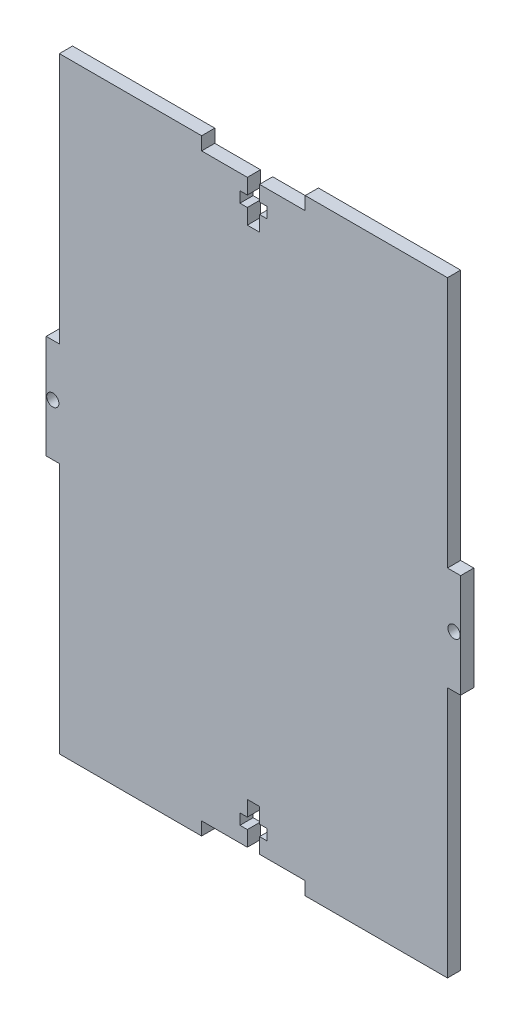
SolidWorks part; units mm, degrees
ref_plane "Front Plane" through (0, 0, 0) normal (0, 0, 1) x (1, 0, 0)
ref_plane "Top Plane" through (0, 0, 0) normal (0, 1, 0) x (1, 0, 0)
ref_plane "Right Plane" through (0, 0, 0) normal (1, 0, 0) x (0, 0, -1)
sketch "Sketch1" plane through (0, 0, 0) normal (0, 0, 1) x (1, 0, 0)
  line L0 (0, 73.175) -> (0, -73.175) construction
  line L1 (-46.825, 73.175) -> (46.825, 73.175)
  line L2 (-46.825, 73.175) -> (-46.825, -73.175)
  line L3 (-46.825, -73.175) -> (46.825, -73.175)
  line L4 (46.825, 73.175) -> (46.825, -73.175)
  line L5 (-46.825, 73.175) -> (46.825, -73.175) construction
  line L6 (-46.825, -73.175) -> (46.825, 73.175) construction
  line L7 (-46.825, 0) -> (46.825, 0) construction
  line L8 (-3.25, -63.7) -> (3.25, -63.7)
  line L9 (12.5, 73.175) -> (-12.5, 73.175)
  line L10 (12.5, 73.175) -> (12.5, 70)
  line L11 (12.5, 70) -> (-12.5, 70)
  line L12 (-12.5, 73.175) -> (-12.5, 70)
  line L13 (12.5, 73.175) -> (-12.5, 70) construction
  line L14 (12.5, 70) -> (-12.5, 73.175) construction
  line L15 (-1.47, 70) -> (1.47, 70)
  line L16 (-1.47, 70) -> (-1.47, 60)
  line L17 (-1.47, 60) -> (1.47, 60)
  line L18 (1.47, 70) -> (1.47, 60)
  line L19 (-1.47, 70) -> (1.47, 60) construction
  line L20 (-1.47, 60) -> (1.47, 70) construction
  line L21 (-3.25, 66.3) -> (3.25, 66.3)
  line L22 (-3.25, 66.3) -> (-3.25, 63.7)
  line L23 (-3.25, 63.7) -> (3.25, 63.7)
  line L24 (3.25, 66.3) -> (3.25, 63.7)
  line L25 (-3.25, 66.3) -> (3.25, 63.7) construction
  line L26 (-3.25, 63.7) -> (3.25, 66.3) construction
  line L27 (3.25, -66.3) -> (3.25, -63.7)
  line L28 (-3.25, -66.3) -> (3.25, -66.3)
  line L29 (-3.25, -66.3) -> (-3.25, -63.7)
  line L30 (-1.47, -60) -> (1.47, -60)
  line L31 (1.47, -70) -> (1.47, -60)
  line L32 (-1.47, -70) -> (1.47, -70)
  line L33 (-1.47, -70) -> (-1.47, -60)
  line L34 (12.5, -70) -> (-12.5, -70)
  line L35 (-12.5, -73.175) -> (-12.5, -70)
  line L36 (12.5, -73.175) -> (-12.5, -73.175)
  line L37 (12.5, -73.175) -> (12.5, -70)
  line L38 (50, -12.5) -> (46.825, -12.5)
  line L39 (-50, 12.5) -> (-46.825, 12.5)
  line L40 (-50, 12.5) -> (-50, -12.5)
  line L41 (-50, -12.5) -> (-46.825, -12.5)
  line L42 (-46.825, 12.5) -> (-46.825, -12.5)
  line L43 (-50, 12.5) -> (-46.825, -12.5) construction
  line L44 (-50, -12.5) -> (-46.825, 12.5) construction
  line L45 (46.825, 12.5) -> (46.825, -12.5)
  line L46 (50, 12.5) -> (46.825, 12.5)
  line L47 (50, 12.5) -> (50, -12.5)
  circle A0 centre (-48.4125, 0) radius 1.47
  circle A1 centre (48.4125, 0) radius 1.47
  point P0 (0, 0)
  point P10 (0, 71.5875)
  point P15 (0, 65)
  point P20 (0, 65)
  point P37 (-48.4125, 0)
  dimension "D11" = 2.94
  dimension "D1" = 146.35
  dimension "D2" = 93.65
  dimension "D3" = 3.175
  dimension "D4" = 10
  dimension "D5" = 2.94
  dimension "D6" = 25
  dimension "D7" = 6.5
  dimension "D8" = 2.6
  dimension "D9" = 6.3
  dimension "D10" = 3.175
extrude "Boss-Extrude1" add sketch "Sketch1" along normal mid plane 3.175 contours L21 L24 L23 L18 L17 L16 L22 L11 L12 L1 L2 L3 L4 L10 | L40 L39 L42 L41 | A0 | L38 L45 L46 L47 | A1
